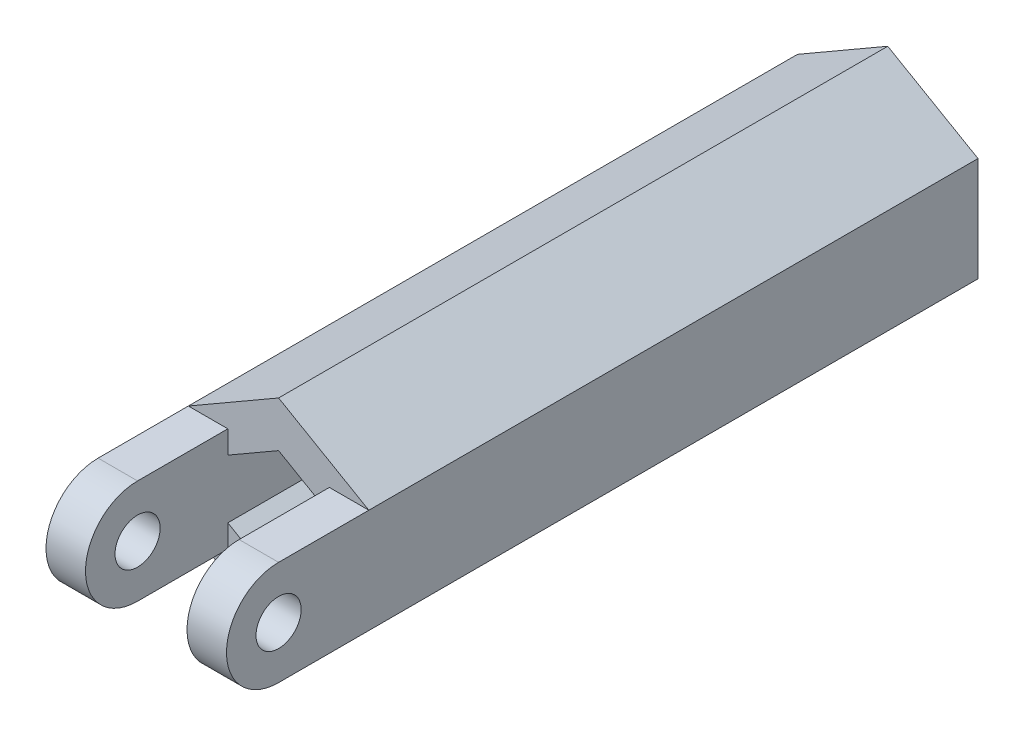
SolidWorks part; units mm, degrees
ref_plane "정면" through (0, 0, 0) normal (0, 0, 1) x (1, 0, 0)
ref_plane "윗면" through (0, 0, 0) normal (0, 1, 0) x (1, 0, 0)
ref_plane "우측면" through (0, 0, 0) normal (1, 0, 0) x (0, 0, -1)
sketch "스케치1" plane through (0, 0, 0) normal (0, 0, 1) x (1, 0, 0)
  line L1 (0, 2.5981) -> (-2.25, 1.299)
  line L2 (-2.25, 1.299) -> (-2.25, -1.299)
  line L3 (-2.25, -1.299) -> (0, -2.5981)
  line L4 (0, -2.5981) -> (2.25, -1.299)
  line L5 (2.25, -1.299) -> (2.25, 1.299)
  line L6 (2.25, 1.299) -> (0, 2.5981)
  line L7 (0, 4.6188) -> (-4, 2.3094)
  line L8 (-4, 2.3094) -> (-4, -2.3094)
  line L9 (-4, -2.3094) -> (0, -4.6188)
  line L10 (0, -4.6188) -> (4, -2.3094)
  line L11 (4, -2.3094) -> (4, 2.3094)
  line L12 (4, 2.3094) -> (0, 4.6188)
  circle A0 centre (0, 0) radius 2.25 construction
  circle A1 centre (0, 0) radius 4 construction
  point P1 (0, 0)
  point P17 (2.25, 1.299)
  dimension "D1" = 4.5
  dimension "D2" = 8
extrude "보스-돌출1" add sketch "스케치1" along normal blind 25
sketch "스케치2" plane through (0, 0, 0) normal (0, 0, -1) x (-1, 0, 0)
  line L1 (0, 4.6188) -> (-4, 2.3094)
  line L2 (-4, 2.3094) -> (-4, -2.3094)
  line L3 (-4, -2.3094) -> (0, -4.6188)
  line L4 (0, -4.6188) -> (4, -2.3094)
  line L5 (4, -2.3094) -> (4, 2.3094)
  line L6 (4, 2.3094) -> (0, 4.6188)
  circle A0 centre (0, 0) radius 4 construction
  circle A1 centre (0, 0) radius 1.25
  dimension "D1" = 2.5
extrude "보스-돌출2" add sketch "스케치2" along normal blind 2
sketch "스케치3" plane through (-4, 0, 0) normal (-1, 0, 0) x (0, 0, 1)
  line L0 (25, 2.3094) -> (-2, 2.3094) construction
  line L1 (25, 2.3094) -> (29, 2.3094)
  line L2 (25, 2.3094) -> (25, -2.3094)
  line L3 (25, -2.3094) -> (29, -2.3094)
  line L5 (25, -2.3094) -> (-2, -2.3094) construction
  line L6 (25, 2.3094) -> (25, -2.3094) construction
  arc A0 (29, -2.3094) -> (29, 2.3094) centre (29, 0) ccw
  circle A1 centre (29, 0) radius 1
  point P11 (29, 0)
  dimension "D2" = 2
  dimension "D1" = 4
extrude "보스-돌출3" add sketch "스케치3" against normal up to surface (1.75 mm away) up to face at (-2.25, 0, 12.5)
sketch "스케치4" plane through (4, 0, 0) normal (1, 0, 0) x (0, 0, -1)
  line L0 (-29, 2.3094) -> (-25, 2.3094)
  line L1 (-25, 2.3094) -> (-25, -2.3094)
  line L2 (-25, -2.3094) -> (-29, -2.3094)
  arc A0 (-29, 2.3094) -> (-29, -2.3094) centre (-29, 0) ccw
  circle A1 centre (-29, 0) radius 1
  arc A2 (-29, 2.3094) -> (-29, -2.3094) centre (-29, 0) ccw construction
  circle A3 centre (-29, 0) radius 1 construction
extrude "보스-돌출4" add sketch "스케치4" against normal up to surface (1.75 mm away) up to face at (2.25, 0, 12.5)
